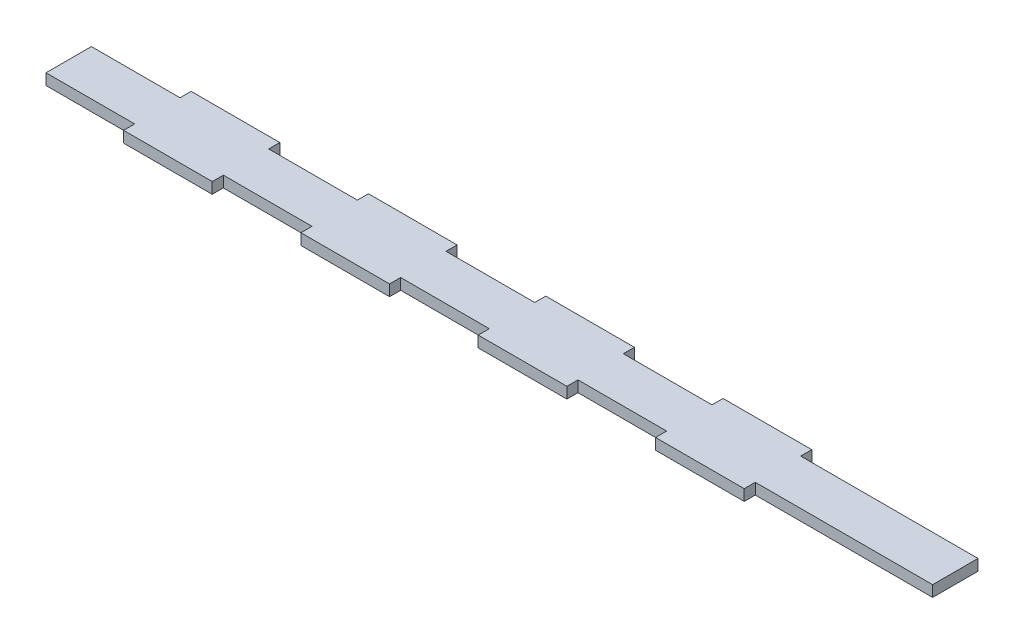
SolidWorks part; units mm, degrees
ref_plane "Front Plane" through (0, 0, 0) normal (0, 0, 1) x (1, 0, 0)
ref_plane "Top Plane" through (0, 0, 0) normal (0, 1, 0) x (1, 0, 0)
ref_plane "Right Plane" through (0, 0, 0) normal (1, 0, 0) x (0, 0, -1)
sketch "Sketch1" plane through (0, 0, 0) normal (0, 1, 0) x (1, 0, 0)
  line L0 (-114.3, 9.675) -> (-88.9, 9.675) construction
  line L1 (-139.7, -6.5) -> (139.7, -6.5)
  line L2 (-139.7, -6.5) -> (-139.7, 6.5)
  line L3 (-139.7, 6.5) -> (139.7, 6.5)
  line L4 (139.7, -6.5) -> (139.7, 6.5)
  line L5 (-139.7, 6.5) -> (-114.3, 6.5)
  line L6 (-139.7, 6.5) -> (-139.7, 9.675)
  line L7 (-139.7, 9.675) -> (-114.3, 9.675)
  line L8 (-114.3, 6.5) -> (-114.3, 9.675)
  line L9 (-88.9, 6.5) -> (-63.5, 6.5)
  line L10 (-88.9, 6.5) -> (-88.9, 9.675)
  line L11 (-88.9, 9.675) -> (-63.5, 9.675)
  line L12 (-63.5, 6.5) -> (-63.5, 9.675)
  line L13 (-38.1, 6.5) -> (-12.7, 6.5)
  line L14 (-38.1, 6.5) -> (-38.1, 9.675)
  line L15 (-38.1, 9.675) -> (-12.7, 9.675)
  line L16 (-12.7, 6.5) -> (-12.7, 9.675)
  line L17 (12.7, 6.5) -> (38.1, 6.5)
  line L18 (12.7, 6.5) -> (12.7, 9.675)
  line L19 (12.7, 9.675) -> (38.1, 9.675)
  line L20 (38.1, 6.5) -> (38.1, 9.675)
  line L21 (63.5, 6.5) -> (88.9, 6.5)
  line L22 (63.5, 6.5) -> (63.5, 9.675)
  line L23 (63.5, 9.675) -> (88.9, 9.675)
  line L24 (88.9, 6.5) -> (88.9, 9.675)
  line L25 (-139.7, -6.5) -> (-114.3, -6.5)
  line L26 (-139.7, -6.5) -> (-139.7, -9.675)
  line L27 (-139.7, -9.675) -> (-114.3, -9.675)
  line L28 (-114.3, -6.5) -> (-114.3, -9.675)
  line L29 (-88.9, -6.5) -> (-63.5, -6.5)
  line L30 (-88.9, -6.5) -> (-88.9, -9.675)
  line L31 (-88.9, -9.675) -> (-63.5, -9.675)
  line L32 (-63.5, -6.5) -> (-63.5, -9.675)
  line L33 (-38.1, -6.5) -> (-12.7, -6.5)
  line L34 (-38.1, -6.5) -> (-38.1, -9.675)
  line L35 (-38.1, -9.675) -> (-12.7, -9.675)
  line L36 (-12.7, -6.5) -> (-12.7, -9.675)
  line L37 (12.7, -6.5) -> (38.1, -6.5)
  line L38 (12.7, -6.5) -> (12.7, -9.675)
  line L39 (12.7, -9.675) -> (38.1, -9.675)
  line L40 (38.1, -6.5) -> (38.1, -9.675)
  line L41 (63.5, -6.5) -> (88.9, -6.5)
  line L42 (63.5, -6.5) -> (63.5, -9.675)
  line L43 (63.5, -9.675) -> (88.9, -9.675)
  line L44 (88.9, -6.5) -> (88.9, -9.675)
  line L45 (-63.5, 9.675) -> (-38.1, 9.675) construction
  line L46 (-12.7, 9.675) -> (12.7, 9.675) construction
  line L47 (38.1, 9.675) -> (63.5, 9.675) construction
  line L48 (-114.3, -9.675) -> (-88.9, -9.675) construction
  line L49 (-63.5, -9.675) -> (-38.1, -9.675) construction
  line L50 (-12.7, -9.675) -> (12.7, -9.675) construction
  line L51 (38.1, -9.675) -> (63.5, -9.675) construction
  line L52 (-114.3, -6.5) -> (-114.3, 6.5)
  point P4 (-139.7, 0)
  point P6 (0, 6.5)
  dimension "D1" = 13
  dimension "D2" = 279.4
  dimension "D3" = 25.4
  dimension "D4" = 3.175
extrude "Boss-Extrude1" add sketch "Sketch1" along normal mid plane 3.175 contours L1 L4 L3 L2 | L3 L12 L11 L10 | L36 L1 L34 L35 | L40 L1 L38 L39 | L44 L1 L42 L43 | L31 L32 L29 L30 | L15 L16 L13 L14 | L19 L20 L17 L18 | L23 L24 L21 L22
